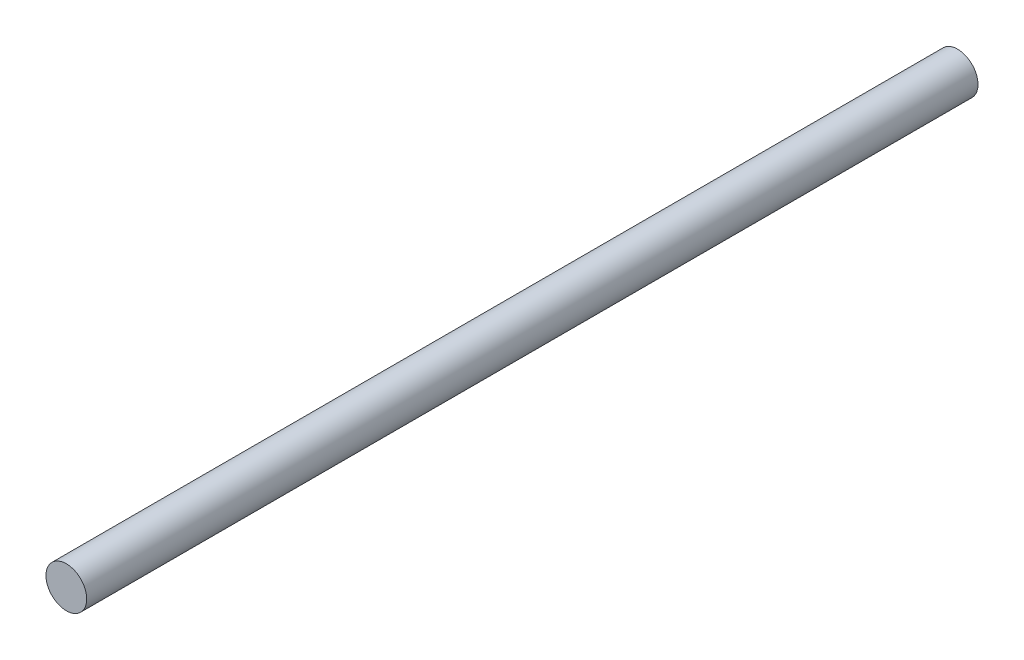
SolidWorks part; units mm, degrees
ref_plane "Front Plane" through (0, 0, 0) normal (0, 0, 1) x (1, 0, 0)
ref_plane "Top Plane" through (0, 0, 0) normal (0, 1, 0) x (1, 0, 0)
ref_plane "Right Plane" through (0, 0, 0) normal (1, 0, 0) x (0, 0, -1)
sketch "Sketch1" plane through (0, 0, 0) normal (0, 0, 1) x (1, 0, 0)
  circle A0 centre (0, 0) radius 4
  dimension "D1" = 8
extrude "Boss-Extrude1" add sketch "Sketch1" along normal blind 175
